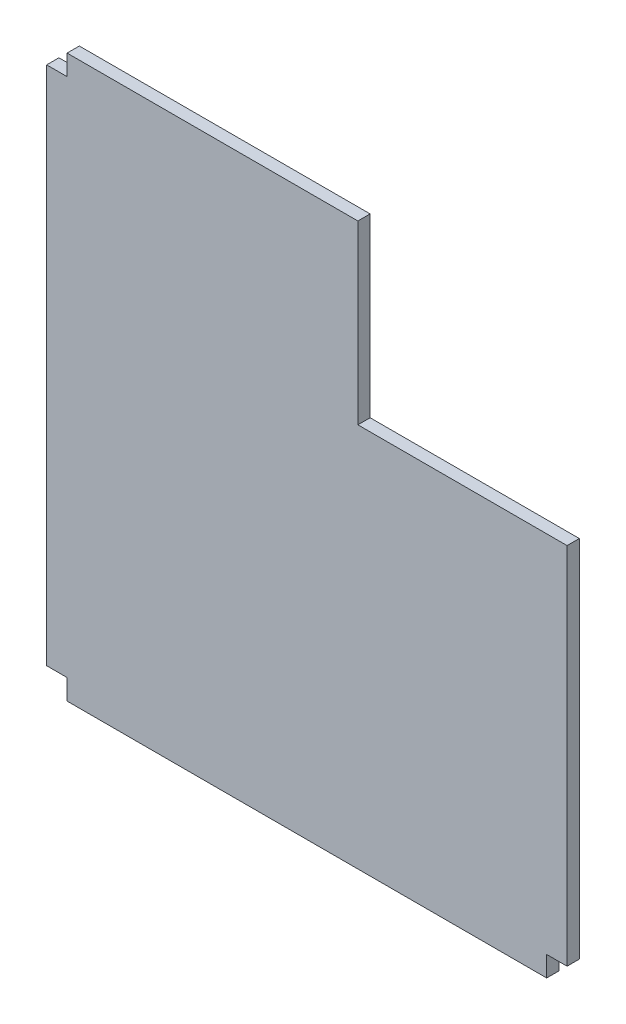
SolidWorks part; units mm, degrees
ref_plane "正面" through (0, 0, 0) normal (0, 0, 1) x (1, 0, 0)
ref_plane "平面" through (0, 0, 0) normal (0, 1, 0) x (1, 0, 0)
ref_plane "右側面" through (0, 0, 0) normal (1, 0, 0) x (0, 0, -1)
sketch "ｽｹｯﾁ1" plane through (0, 0, 0) normal (0, 0, 1) x (1, 0, 0)
  line L1 (-235, 255) -> (235, 255)
  line L2 (-235, 255) -> (-235, -255)
  line L3 (-235, -255) -> (235, -255)
  line L4 (235, 255) -> (235, -255)
  line L5 (-235, 255) -> (235, -255) construction
  line L6 (-235, -255) -> (235, 255) construction
  line L7 (235, 255) -> (255, 255)
  line L8 (235, 255) -> (235, -255)
  line L9 (235, -255) -> (255, -255)
  line L10 (255, 255) -> (255, -255)
  line L11 (235, -255) -> (-235, -255)
  line L12 (235, -255) -> (235, -275)
  line L13 (235, -275) -> (-235, -275)
  line L14 (-235, -255) -> (-235, -275)
  line L15 (-235, -255) -> (-255, -255)
  line L16 (-235, -255) -> (-235, 255)
  line L17 (-235, 255) -> (-255, 255)
  line L18 (-255, -255) -> (-255, 255)
  line L19 (-235, 255) -> (235, 255)
  line L20 (-235, 255) -> (-235, 275)
  line L21 (-235, 275) -> (235, 275)
  line L22 (235, 255) -> (235, 275)
  point P0 (0, 0)
  dimension "D1" = 510
  dimension "D2" = 470
  dimension "D3" = 20
  dimension "D4" = 20
  dimension "D5" = 20
  dimension "D6" = 20
extrude "ﾎﾞｽ - 押し出し1" add sketch "ｽｹｯﾁ1" along normal blind 12 contours L4 L1 L2 L3 | L1 L22 L21 L20 | L18 L15 L2 L17 | L10 L7 L4 L9 | L3 L14 L13 L12
sketch "ｽｹｯﾁ2" plane through (0, 0, 0) normal (0, 0, -1) x (-1, 0, 0)
  line L1 (-235, 255) -> (-50, 255)
  line L2 (-235, 255) -> (-235, 102)
  line L3 (-235, 102) -> (-50, 102)
  line L4 (-50, 255) -> (-50, 102)
  line L5 (-50, 102) -> (-364.6973, 102)
  line L6 (-50, 102) -> (-50, 308.5874)
  line L7 (-50, 308.5874) -> (-364.6973, 308.5874)
  line L8 (-364.6973, 102) -> (-364.6973, 308.5874)
  line M10 (235, 275) -> (-235, 275)
  line M11 (-235, 275) -> (-235, 255)
  line M12 (-235, 255) -> (-255, 255)
  line M13 (-255, 255) -> (-255, -255)
  dimension "D1" = 153
  dimension "D2" = 185
extrude "ｶｯﾄ - 押し出し1" cut sketch "ｽｹｯﾁ2" against normal blind 12 contours L8 L5 L6 L7 M13 M12 M11 M10 | L4 L1 L2 L3 | L5 L2 M12 M13 | L1 L6 M10 M11
